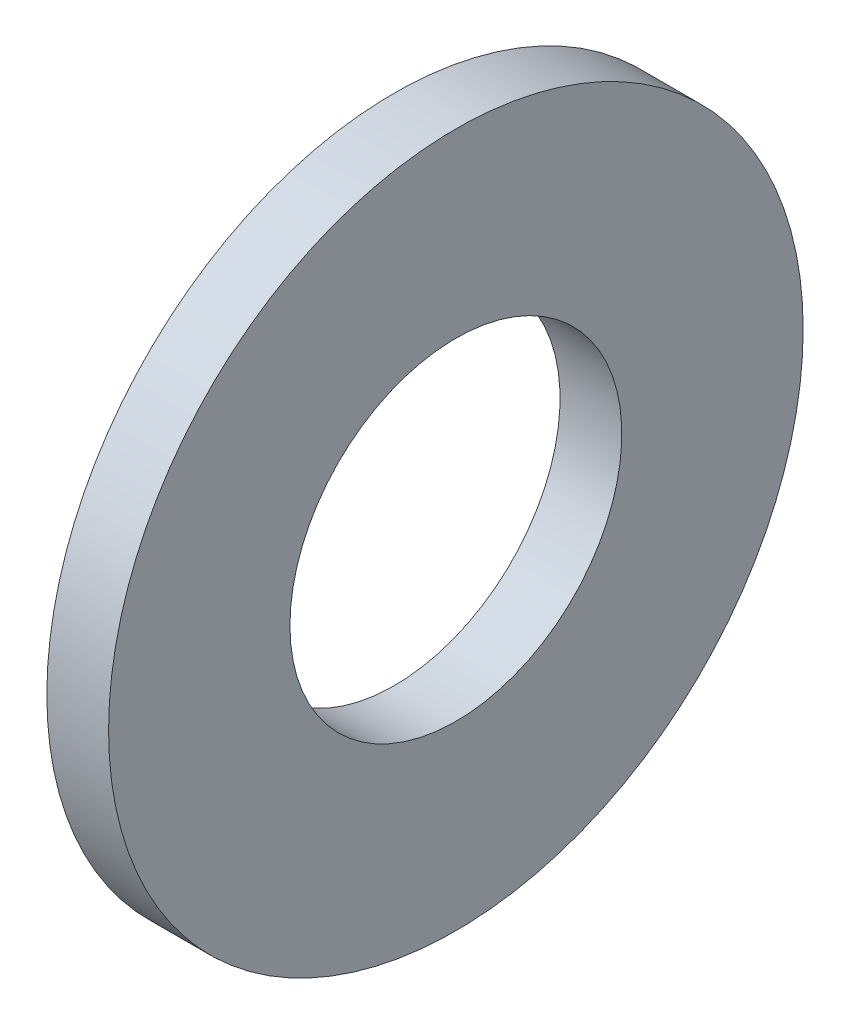
SolidWorks part; units mm, degrees
ref_plane "Plane1" through (0, 0, 0) normal (0, 0, 1) x (1, 0, 0)
ref_plane "Plane2" through (0, 0, 0) normal (0, 1, 0) x (1, 0, 0)
ref_plane "Plane3" through (0, 0, 0) normal (1, 0, 0) x (0, 0, -1)
sketch "Sketch1" plane through (0, 0, 0) normal (0, 0, 1) x (1, 0, 0)
  line L0 (-34.925, 0) -> (9.525, 0) construction
  line L1 (0, 2.15) -> (0, 4.5)
  line L2 (0, 4.5) -> (-0.8, 4.5)
  line L3 (-0.8, 4.5) -> (-0.8, 2.15)
  line L4 (-0.8, 2.15) -> (0, 2.15)
  dimension "Thickness" = 0.8
  dimension "Inside_dia" = 4.3
  dimension "Outside_dia" = 9
revolve "Base-Revolve" add sketch "Sketch1" angle 360 about L0
chamfer "ODChamfer" [suppressed] distance 0.2 angle 45
equation "\"D1@ODChamfer\" =  \"Thickness@Sketch1\" * 0.25"
